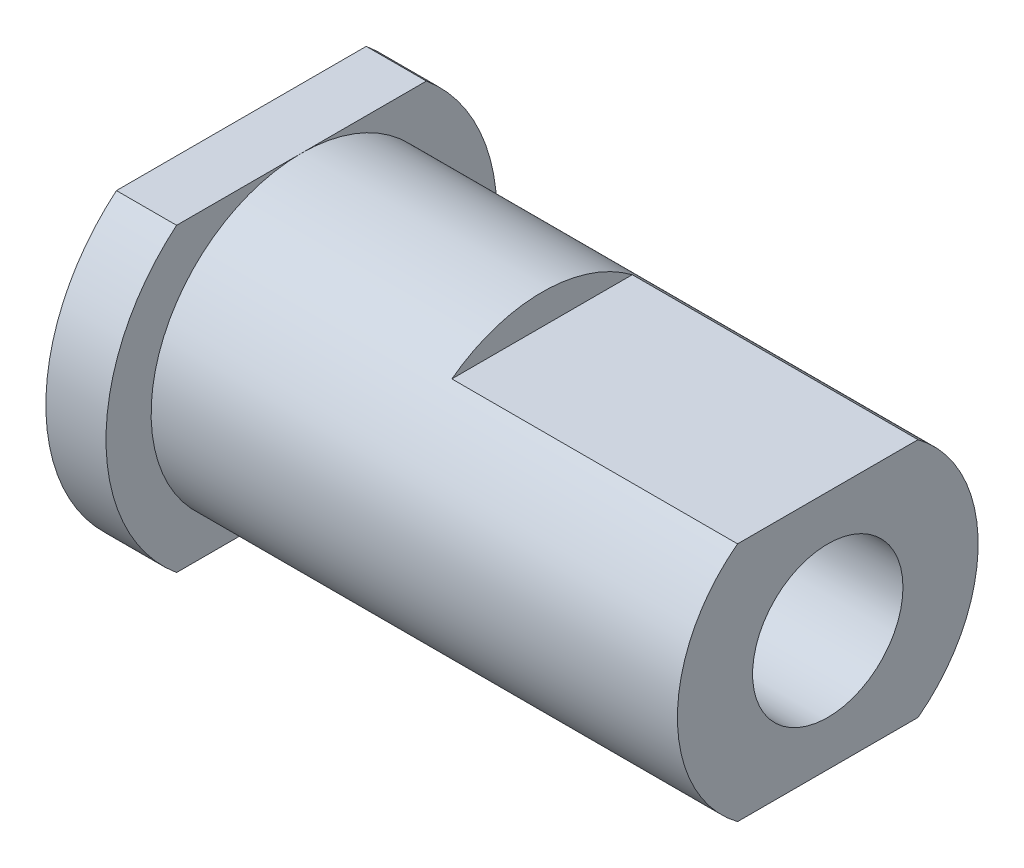
SolidWorks part; units mm, degrees
material "Brass"
ref_plane "Front Plane" through (0, 0, 0) normal (0, 0, 1) x (1, 0, 0)
ref_plane "Top Plane" through (0, 0, 0) normal (0, 1, 0) x (1, 0, 0)
ref_plane "Right Plane" through (0, 0, 0) normal (1, 0, 0) x (0, 0, -1)
sketch "Sketch1" plane through (0, 0, 0) normal (1, 0, 0) x (0, 0, -1)
  line L1 (-4.1533, -5) -> (4.1533, -5)
  line L2 (-4.1533, -5) -> (-4.1533, 5)
  line L3 (-4.1533, 5) -> (4.1533, 5)
  line L4 (4.1533, -5) -> (4.1533, 5)
  line L5 (-4.1533, -5) -> (4.1533, 5) construction
  line L6 (-4.1533, 5) -> (4.1533, -5) construction
  arc A0 (-4.1533, 5) -> (-4.1533, -5) centre (0, 0) ccw
  arc A1 (4.1533, -5) -> (4.1533, 5) centre (0, 0) ccw
  dimension "D1" = 13
  dimension "D2" = 10
extrude "Boss-Extrude1" add sketch "Sketch1" along normal blind 2 contours L2 A0 | L1 L4 L3 L2 | L4 A1
sketch "Sketch2" plane through (2, 0, 0) normal (1, 0, 0) x (0, 0, -1)
  circle A0 centre (0, 0) radius 5
  dimension "D1" = 10
extrude "Boss-Extrude2" add sketch "Sketch2" along normal blind 8
sketch "Sketch3" plane through (10, 0, 0) normal (1, 0, 0) x (0, 0, -1)
  line L1 (-3, -4) -> (3, -4)
  line L2 (-3, -4) -> (-3, 4)
  line L3 (-3, 4) -> (3, 4)
  line L4 (3, -4) -> (3, 4)
  line L5 (-3, -4) -> (3, 4) construction
  line L6 (-3, 4) -> (3, -4) construction
  circle A0 centre (0, 0) radius 5 construction
  circle A1 centre (0, 0) radius 5
  circle M1 centre (0, 0) radius 5
  dimension "D1" = 8
extrude "Boss-Extrude3" add sketch "Sketch3" along normal blind 9.5 contours L2 M1 | L1 L4 L3 L2 | L4 M1
sketch "Sketch4" plane through (19.5, 0, 0) normal (1, 0, 0) x (0, 0, -1)
  circle A0 centre (0, 0) radius 2.5
  dimension "D1" = 5
extrude "Cut-Extrude1" cut sketch "Sketch4" against normal through all
equation "\"e\"=4.82414"
